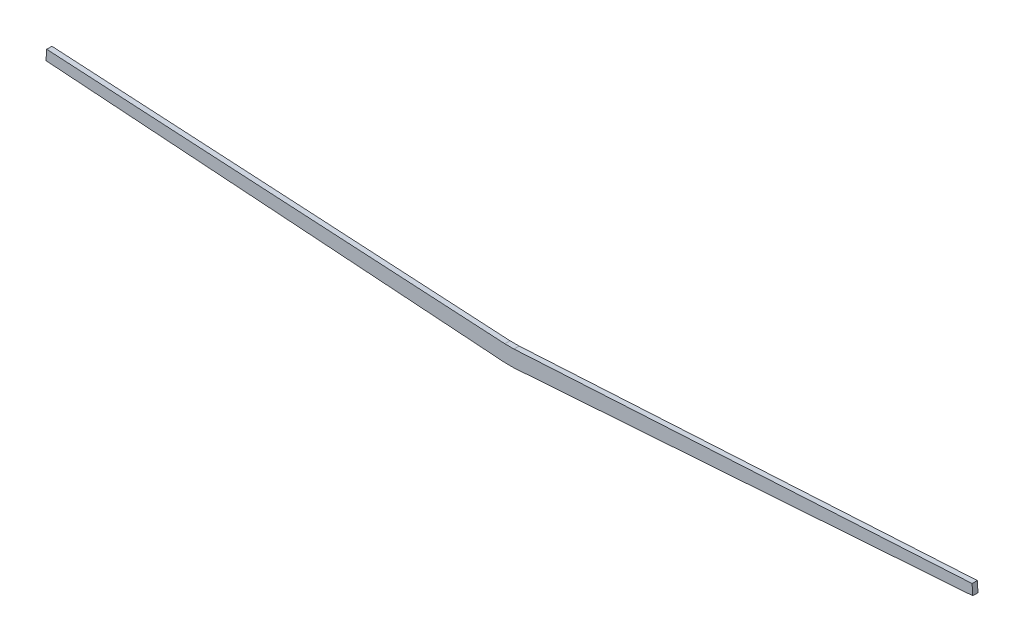
SolidWorks part; units mm, degrees
ref_plane "Front Plane" through (0, 0, 0) normal (0, 0, 1) x (1, 0, 0)
ref_plane "Top Plane" through (0, 0, 0) normal (0, 1, 0) x (1, 0, 0)
ref_plane "Right Plane" through (0, 0, 0) normal (1, 0, 0) x (0, 0, -1)
sketch "Sketch1" plane through (0, 0, 0) normal (0, 0, 1) x (1, 0, 0)
  line L0 (-641.3218, 44.4016) -> (-6.35, 0)
  line L1 (-6.35, 0) -> (6.35, 0)
  line L2 (6.35, 0) -> (641.3218, 44.4016)
  line L3 (641.3218, 44.4016) -> (640.3296, 58.5909)
  line L4 (640.3296, 58.5909) -> (6.35, 22.606)
  line L5 (6.35, 22.606) -> (-6.35, 22.606)
  line L6 (-6.35, 22.606) -> (-640.3296, 58.5909)
  line L7 (-640.3296, 58.5909) -> (-641.3218, 44.4016)
  point P7 (-78.7766, 29.4244)
  point P9 (-8.3811, 18.9034)
  point P10 (131.5454, 12.5899)
  point P12 (0, 0)
  point P13 (0, 22.606)
  point P14 (2.2704, 1.01)
  point P15 (0, 0)
  point P16 (0, 0)
  point P17 (0, 0)
  point P18 (7.9676, -0.7026)
  dimension "D1" = 14.224
  dimension "D2" = 22.606
  dimension "D3" = 635
  dimension "D4" = 4
  dimension "D5" = 12.7
extrude "Boss-Extrude1" add sketch "Sketch1" along normal blind 7.2
